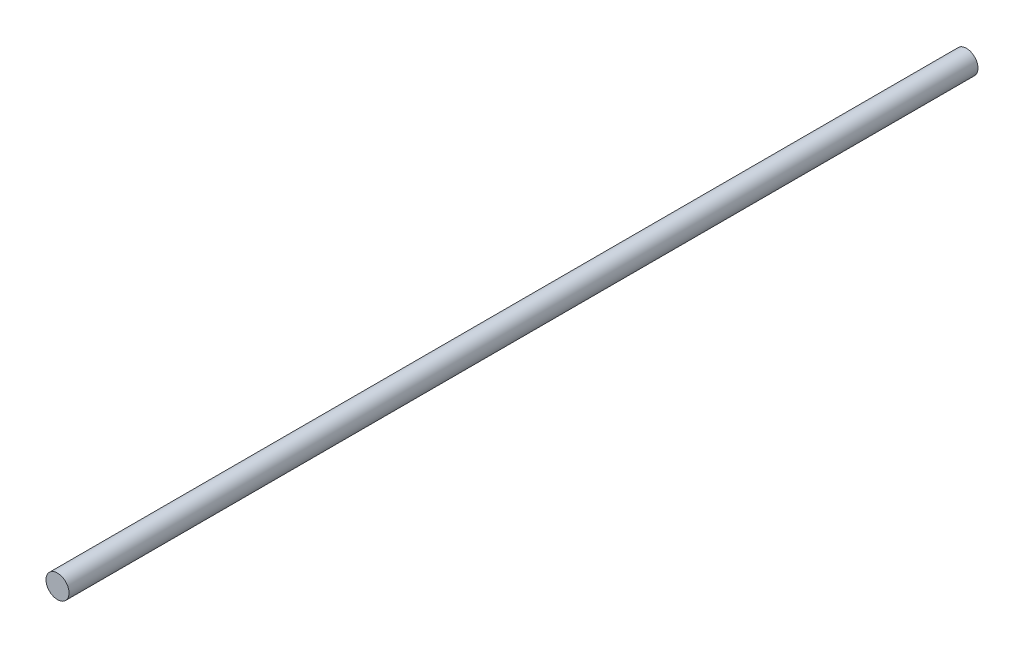
SolidWorks part; units mm, degrees
ref_plane "Front Plane" through (0, 0, 0) normal (0, 0, 1) x (1, 0, 0)
ref_plane "Top Plane" through (0, 0, 0) normal (0, 1, 0) x (1, 0, 0)
ref_plane "Right Plane" through (0, 0, 0) normal (1, 0, 0) x (0, 0, -1)
sketch "Sketch1" plane through (0, 0, 0) normal (0, 0, 1) x (1, 0, 0)
  circle A0 centre (0, 0) radius 0.5
  dimension "D1" = 1
extrude "Rod" add sketch "Sketch1" along normal blind 39.44
